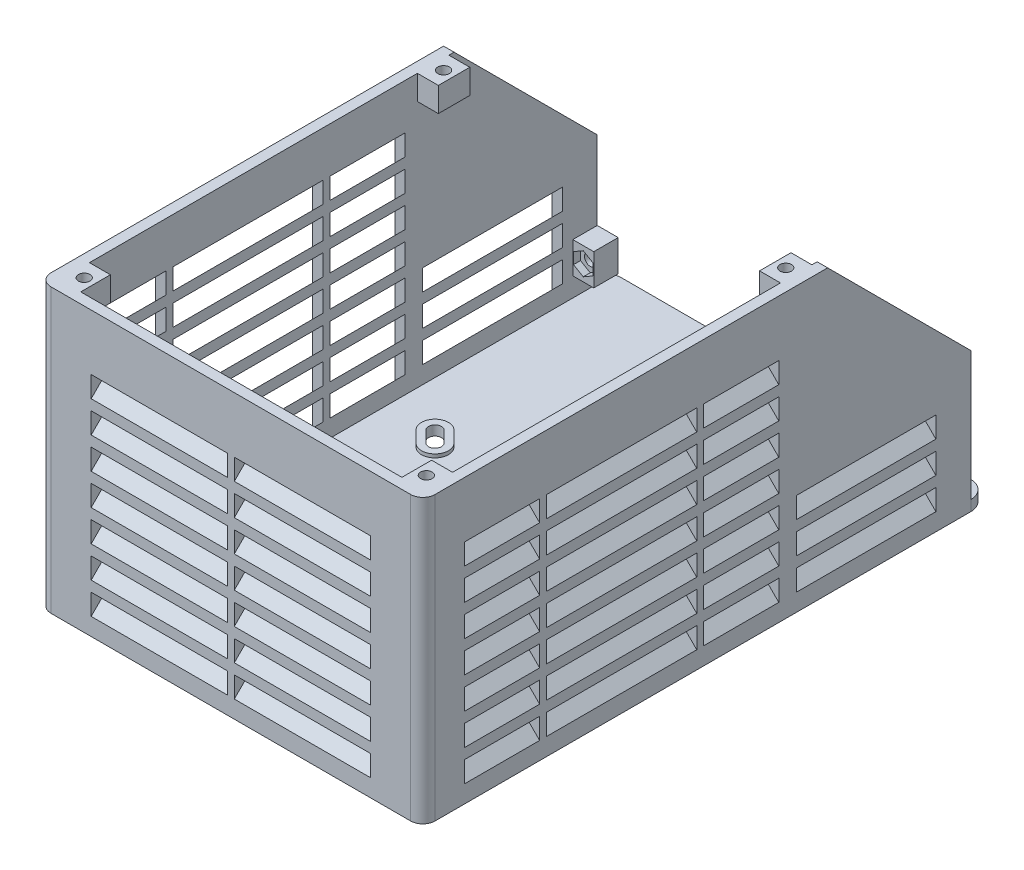
SolidWorks part; units mm, degrees
ref_plane "前视基准面" through (0, 0, 0) normal (0, 0, 1) x (1, 0, 0)
ref_plane "上视基准面" through (0, 0, 0) normal (0, 1, 0) x (1, 0, 0)
ref_plane "右视基准面" through (0, 0, 0) normal (1, 0, 0) x (0, 0, -1)
sketch "草图2" plane through (0, 0, 0) normal (0, 1, 0) x (1, 0, 0)
  line L5 (-55, -80.9767) -> (55, -80.9767)
  line L6 (-55, -80.9767) -> (-55, 80.9767)
  line L7 (-37.4767, -59.9767) -> (37.4767, -59.9767) construction
  line L8 (-37.4767, -59.9767) -> (-37.4767, 14.9767) construction
  line L9 (-37.4767, 14.9767) -> (37.4767, 14.9767) construction
  line L10 (37.4767, -59.9767) -> (37.4767, 14.9767) construction
  line L11 (-37.4767, -59.9767) -> (37.4767, 14.9767) construction
  line L12 (-37.4767, 14.9767) -> (37.4767, -59.9767) construction
  line L13 (-55, 80.9767) -> (55, 80.9767)
  line L14 (55, -80.9767) -> (55, 80.9767)
  line L15 (-55, -80.9767) -> (55, 80.9767) construction
  line L16 (-55, 80.9767) -> (55, -80.9767) construction
  circle A0 centre (-37.4767, 14.9767) radius 1.75
  circle A1 centre (-37.4767, -59.9767) radius 1.75
  circle A2 centre (37.4767, -59.9767) radius 1.75
  circle A3 centre (37.4767, 14.9767) radius 1.75
  point P0 (0, 0)
  point P6 (0, -22.5)
  dimension "D2" = 3.5
  dimension "D1" = 106
  dimension "D3" = 66
  dimension "D4" = 110
  dimension "D5" = 21
extrude "凸台-拉伸1" add sketch "草图2" along normal blind 3
fillet "圆角1" radius 3.5 2 edges at (-55, 1.5, 80.9767) (55, 1.5, 80.9767)
fillet "圆角2" radius 5 2 edges at (-55, 1.5, -80.9767) (55, 1.5, -80.9767)
sketch "草图3" plane through (0, 3, 0) normal (0, 1, 0) x (1, 0, 0)
  line L7 (-55, 75.9767) -> (-55, -77.4767) construction
  line L17 (55, -77.4767) -> (55, 75.9767) construction
  line L18 (-51.5, -80.9767) -> (51.5, -80.9767) construction
  line L19 (-52, 75.9767) -> (-52, -77.4767)
  line L20 (52, -77.4767) -> (52, 75.9767)
  line L21 (-51.5, -77.9767) -> (51.5, -77.9767)
  line L22 (-52, 75.9767) -> (-52, -77.4767)
  line L23 (52, -77.4767) -> (52, 75.9767)
  line L24 (-51.5, -77.9767) -> (51.5, -77.9767)
  line L25 (-55, 75.9767) -> (-55, -77.4767)
  line L26 (55, -77.4767) -> (55, 75.9767)
  line L27 (-51.5, -80.9767) -> (51.5, -80.9767)
  line L28 (55, 75.9767) -> (52, 75.9767)
  line L29 (-52, 75.9767) -> (-55, 75.9767)
  arc A2 (-55, -77.4767) -> (-51.5, -80.9767) centre (-51.5, -77.4767) ccw construction
  arc A3 (51.5, -80.9767) -> (55, -77.4767) centre (51.5, -77.4767) ccw construction
  arc A4 (-52, -77.4767) -> (-51.5, -77.9767) centre (-51.5, -77.4767) ccw
  arc A5 (51.5, -77.9767) -> (52, -77.4767) centre (51.5, -77.4767) ccw
  arc A6 (-52, -77.4767) -> (-51.5, -77.9767) centre (-51.5, -77.4767) ccw
  arc A7 (51.5, -77.9767) -> (52, -77.4767) centre (51.5, -77.4767) ccw
  arc A8 (-55, -77.4767) -> (-51.5, -80.9767) centre (-51.5, -77.4767) ccw
  arc A9 (51.5, -80.9767) -> (55, -77.4767) centre (51.5, -77.4767) ccw
  dimension "D1" = 3
extrude "凸台-拉伸2" add sketch "草图3" along normal blind 78
sketch "草图4" plane through (55, 0, 0) normal (1, 0, 0) x (0, 0, -1)
  line L0 (75.9767, 81) -> (75.9767, 39.9878)
  line L1 (75.9767, 81) -> (75.9767, 3) construction
  line L2 (75.9767, 39.9878) -> (34.9645, 81)
  line L3 (-77.4767, 81) -> (75.9767, 81) construction
  line L4 (34.9645, 81) -> (75.9767, 81)
  dimension "D1" = 45
  dimension "D2" = 58
extrude "切除-拉伸1" cut sketch "草图4" against normal through all
sketch "草图16" plane through (0, 0, 0) normal (0, -1, 0) x (1, 0, 0)
  line L0 (-37.9716, 60.4716) -> (-34.7897, 57.2897) construction
  line L4 (-36.6635, 61.7798) -> (-33.4815, 58.5978)
  line L5 (-39.2798, 59.1635) -> (-36.0978, 55.9815)
  line L6 (-37.4767, 59.9767) -> (37.4767, -14.9767) construction
  line L7 (37.9716, 60.4716) -> (34.7897, 57.2897) construction
  line L8 (39.2798, 59.1635) -> (36.0978, 55.9815)
  line L9 (36.6635, 61.7798) -> (33.4815, 58.5978)
  line L10 (37.9716, -15.4716) -> (34.7897, -12.2897) construction
  line L11 (36.6635, -16.7798) -> (33.4815, -13.5978)
  line L12 (39.2798, -14.1635) -> (36.0978, -10.9815)
  line L13 (-37.9716, -15.4716) -> (-34.7897, -12.2897) construction
  line L14 (-39.2798, -14.1635) -> (-36.0978, -10.9815)
  line L15 (-36.6635, -16.7798) -> (-33.4815, -13.5978)
  line L16 (0, 22.5) -> (-37.9716, 60.4716) construction
  arc A2 (-36.6635, 61.7798) -> (-39.2798, 59.1635) centre (-37.9716, 60.4716) ccw
  arc A3 (-36.0978, 55.9815) -> (-33.4815, 58.5978) centre (-34.7897, 57.2897) ccw
  circle A5 centre (-37.4767, 59.9767) radius 1.75 construction
  arc A6 (39.2798, 59.1635) -> (36.6635, 61.7798) centre (37.9716, 60.4716) ccw
  arc A7 (33.4815, 58.5978) -> (36.0978, 55.9815) centre (34.7897, 57.2897) ccw
  arc A8 (36.6635, -16.7798) -> (39.2798, -14.1635) centre (37.9716, -15.4716) ccw
  arc A9 (36.0978, -10.9815) -> (33.4815, -13.5978) centre (34.7897, -12.2897) ccw
  arc A10 (-39.2798, -14.1635) -> (-36.6635, -16.7798) centre (-37.9716, -15.4716) ccw
  arc A11 (-33.4815, -13.5978) -> (-36.0978, -10.9815) centre (-34.7897, -12.2897) ccw
  point P2 (-36.3806, 58.8806)
  point P18 (36.3806, 58.8806)
  point P25 (36.3806, -13.8806)
  point P32 (-36.3806, -13.8806)
  dimension "D3" = 0.1
  dimension "D1" = 0.7
  dimension "D2" = 4.5
  dimension "D5" = 53.7
  dimension "D4" = 4
extrude "切除-拉伸8" cut sketch "草图16" against normal through all
sketch "草图9" plane through (0, 3, 0) normal (0, 1, 0) x (1, 0, 0)
  line L0 (39.2798, 14.1635) -> (36.0978, 10.9815) construction
  line L1 (33.4815, 13.5978) -> (36.6635, 16.7798) construction
  line L2 (-36.0978, 10.9815) -> (-39.2798, 14.1635) construction
  line L3 (-36.6635, 16.7798) -> (-33.4815, 13.5978) construction
  line L4 (39.2798, 14.1635) -> (36.0978, 10.9815)
  line L5 (33.4815, 13.5978) -> (36.6635, 16.7798)
  line L6 (-36.0978, 10.9815) -> (-39.2798, 14.1635)
  line L7 (-36.6635, 16.7798) -> (-33.4815, 13.5978)
  line L8 (36.0978, -55.9815) -> (39.2798, -59.1635) construction
  line L9 (36.6635, -61.7798) -> (33.4815, -58.5978) construction
  line L10 (-39.2798, -59.1635) -> (-36.0978, -55.9815) construction
  line L11 (-33.4815, -58.5978) -> (-36.6635, -61.7798) construction
  line L12 (36.0978, -55.9815) -> (39.2798, -59.1635)
  line L13 (36.6635, -61.7798) -> (33.4815, -58.5978)
  line L14 (-39.2798, -59.1635) -> (-36.0978, -55.9815)
  line L15 (-33.4815, -58.5978) -> (-36.6635, -61.7798)
  line L16 (40.694, 12.7493) -> (37.512, 9.5673)
  line L17 (32.0673, 15.012) -> (35.2493, 18.194)
  line L18 (-37.512, 9.5673) -> (-40.694, 12.7493)
  line L19 (-35.2493, 18.194) -> (-32.0673, 15.012)
  line L20 (37.512, -54.5673) -> (40.694, -57.7493)
  line L21 (35.2493, -63.194) -> (32.0673, -60.012)
  line L22 (-40.694, -57.7493) -> (-37.512, -54.5673)
  line L23 (-32.0673, -60.012) -> (-35.2493, -63.194)
  arc A12 (33.4815, 13.5978) -> (36.0978, 10.9815) centre (34.7897, 12.2897) ccw construction
  arc A13 (39.2798, 14.1635) -> (36.6635, 16.7798) centre (37.9716, 15.4716) ccw construction
  arc A14 (-36.0978, 10.9815) -> (-33.4815, 13.5978) centre (-34.7897, 12.2897) ccw construction
  arc A15 (-36.6635, 16.7798) -> (-39.2798, 14.1635) centre (-37.9716, 15.4716) ccw construction
  arc A16 (33.4815, 13.5978) -> (36.0978, 10.9815) centre (34.7897, 12.2897) ccw
  arc A17 (39.2798, 14.1635) -> (36.6635, 16.7798) centre (37.9716, 15.4716) ccw
  arc A18 (-36.0978, 10.9815) -> (-33.4815, 13.5978) centre (-34.7897, 12.2897) ccw
  arc A19 (-36.6635, 16.7798) -> (-39.2798, 14.1635) centre (-37.9716, 15.4716) ccw
  arc A20 (36.6635, -61.7798) -> (39.2798, -59.1635) centre (37.9716, -60.4716) ccw construction
  arc A21 (36.0978, -55.9815) -> (33.4815, -58.5978) centre (34.7897, -57.2897) ccw construction
  arc A22 (-39.2798, -59.1635) -> (-36.6635, -61.7798) centre (-37.9716, -60.4716) ccw construction
  arc A23 (-33.4815, -58.5978) -> (-36.0978, -55.9815) centre (-34.7897, -57.2897) ccw construction
  arc A24 (36.6635, -61.7798) -> (39.2798, -59.1635) centre (37.9716, -60.4716) ccw
  arc A25 (36.0978, -55.9815) -> (33.4815, -58.5978) centre (34.7897, -57.2897) ccw
  arc A26 (-39.2798, -59.1635) -> (-36.6635, -61.7798) centre (-37.9716, -60.4716) ccw
  arc A27 (-33.4815, -58.5978) -> (-36.0978, -55.9815) centre (-34.7897, -57.2897) ccw
  arc A28 (32.0673, 15.012) -> (37.512, 9.5673) centre (34.7897, 12.2897) ccw
  arc A29 (40.694, 12.7493) -> (35.2493, 18.194) centre (37.9716, 15.4716) ccw
  arc A30 (-35.2493, 18.194) -> (-40.694, 12.7493) centre (-37.9716, 15.4716) ccw
  arc A31 (-37.512, 9.5673) -> (-32.0673, 15.012) centre (-34.7897, 12.2897) ccw
  arc A32 (35.2493, -63.194) -> (40.694, -57.7493) centre (37.9716, -60.4716) ccw
  arc A33 (37.512, -54.5673) -> (32.0673, -60.012) centre (34.7897, -57.2897) ccw
  arc A34 (-32.0673, -60.012) -> (-37.512, -54.5673) centre (-34.7897, -57.2897) ccw
  arc A35 (-40.694, -57.7493) -> (-35.2493, -63.194) centre (-37.9716, -60.4716) ccw
  dimension "D1" = 2
sketch "草图17" plane through (0, 0, 0) normal (0, -1, 0) x (1, 0, 0)
  line L0 (33.4815, -13.5978) -> (36.6635, -16.7798) construction
  line L1 (39.2798, -14.1635) -> (36.0978, -10.9815) construction
  line L2 (-36.0978, -10.9815) -> (-39.2798, -14.1635) construction
  line L3 (-36.6635, -16.7798) -> (-33.4815, -13.5978) construction
  line L4 (36.0978, 55.9815) -> (39.2798, 59.1635) construction
  line L5 (36.6635, 61.7798) -> (33.4815, 58.5978) construction
  line L6 (-39.2798, 59.1635) -> (-36.0978, 55.9815) construction
  line L7 (-33.4815, 58.5978) -> (-36.6635, 61.7798) construction
  line L8 (33.4815, -13.5978) -> (36.6635, -16.7798)
  line L9 (39.2798, -14.1635) -> (36.0978, -10.9815)
  line L10 (-36.0978, -10.9815) -> (-39.2798, -14.1635)
  line L11 (-36.6635, -16.7798) -> (-33.4815, -13.5978)
  line L12 (36.0978, 55.9815) -> (39.2798, 59.1635)
  line L13 (36.6635, 61.7798) -> (33.4815, 58.5978)
  line L14 (-39.2798, 59.1635) -> (-36.0978, 55.9815)
  line L15 (-33.4815, 58.5978) -> (-36.6635, 61.7798)
  line L16 (32.2794, -14.7999) -> (35.4614, -17.9819)
  line L17 (40.4819, -12.9614) -> (37.2999, -9.7794)
  line L18 (-37.2999, -9.7794) -> (-40.4819, -12.9614)
  line L19 (-35.4614, -17.9819) -> (-32.2794, -14.7999)
  line L20 (37.2999, 54.7794) -> (40.4819, 57.9614)
  line L21 (35.4614, 62.9819) -> (32.2794, 59.7999)
  line L22 (-40.4819, 57.9614) -> (-37.2999, 54.7794)
  line L23 (-32.2794, 59.7999) -> (-35.4614, 62.9819)
  arc A0 (36.6635, -16.7798) -> (39.2798, -14.1635) centre (37.9716, -15.4716) ccw construction
  arc A1 (36.0978, -10.9815) -> (33.4815, -13.5978) centre (34.7897, -12.2897) ccw construction
  arc A2 (-39.2798, -14.1635) -> (-36.6635, -16.7798) centre (-37.9716, -15.4716) ccw construction
  arc A3 (-33.4815, -13.5978) -> (-36.0978, -10.9815) centre (-34.7897, -12.2897) ccw construction
  arc A4 (39.2798, 59.1635) -> (36.6635, 61.7798) centre (37.9716, 60.4716) ccw construction
  arc A5 (33.4815, 58.5978) -> (36.0978, 55.9815) centre (34.7897, 57.2897) ccw construction
  arc A6 (-36.0978, 55.9815) -> (-33.4815, 58.5978) centre (-34.7897, 57.2897) ccw construction
  arc A7 (-36.6635, 61.7798) -> (-39.2798, 59.1635) centre (-37.9716, 60.4716) ccw construction
  arc A8 (36.6635, -16.7798) -> (39.2798, -14.1635) centre (37.9716, -15.4716) ccw
  arc A9 (36.0978, -10.9815) -> (33.4815, -13.5978) centre (34.7897, -12.2897) ccw
  arc A10 (-39.2798, -14.1635) -> (-36.6635, -16.7798) centre (-37.9716, -15.4716) ccw
  arc A11 (-33.4815, -13.5978) -> (-36.0978, -10.9815) centre (-34.7897, -12.2897) ccw
  arc A12 (39.2798, 59.1635) -> (36.6635, 61.7798) centre (37.9716, 60.4716) ccw
  arc A13 (33.4815, 58.5978) -> (36.0978, 55.9815) centre (34.7897, 57.2897) ccw
  arc A14 (-36.0978, 55.9815) -> (-33.4815, 58.5978) centre (-34.7897, 57.2897) ccw
  arc A15 (-36.6635, 61.7798) -> (-39.2798, 59.1635) centre (-37.9716, 60.4716) ccw
  arc A16 (35.4614, -17.9819) -> (40.4819, -12.9614) centre (37.9716, -15.4716) ccw
  arc A17 (37.2999, -9.7794) -> (32.2794, -14.7999) centre (34.7897, -12.2897) ccw
  arc A18 (-40.4819, -12.9614) -> (-35.4614, -17.9819) centre (-37.9716, -15.4716) ccw
  arc A19 (-32.2794, -14.7999) -> (-37.2999, -9.7794) centre (-34.7897, -12.2897) ccw
  arc A20 (40.4819, 57.9614) -> (35.4614, 62.9819) centre (37.9716, 60.4716) ccw
  arc A21 (32.2794, 59.7999) -> (37.2999, 54.7794) centre (34.7897, 57.2897) ccw
  arc A22 (-37.2999, 54.7794) -> (-32.2794, 59.7999) centre (-34.7897, 57.2897) ccw
  arc A23 (-35.4614, 62.9819) -> (-40.4819, 57.9614) centre (-37.9716, 60.4716) ccw
  dimension "D1" = 1.7
extrude "切除-拉伸9" cut sketch "草图17" against normal blind 1.2
ref_plane "基准面4" through (0, 0, -20.9767) normal (0, 0, -1) x (-1, 0, 0)
sketch "草图6" plane through (0, 0, -20.9767) normal (0, 0, -1) x (-1, 0, 0)
  line L0 (-55, 65) -> (-52, 68)
  line L1 (-55, 65) -> (-55, 59)
  line L2 (-52, 68) -> (-52, 62)
  line L3 (-55, 59) -> (-52, 62)
  line L4 (-55, 81) -> (-55, 39.9878) construction
  line L5 (-52, 81) -> (-52, 3) construction
  line L6 (-52, 81) -> (-52, 39.9878) construction
  line L7 (-52, 81) -> (-55, 81) construction
  line L44 (0, 0) -> (0, 83.4233) construction
  line L85 (-55, 56) -> (-55, 50)
  line L86 (-55, 56) -> (-52, 59)
  line L87 (-52, 59) -> (-52, 53)
  line L88 (-55, 50) -> (-52, 53)
  line L89 (-55, 47) -> (-55, 41)
  line L90 (-55, 47) -> (-52, 50)
  line L91 (-52, 50) -> (-52, 44)
  line L92 (-55, 41) -> (-52, 44)
  line L93 (-55, 38) -> (-55, 32)
  line L94 (-55, 38) -> (-52, 41)
  line L95 (-52, 41) -> (-52, 35)
  line L96 (-55, 32) -> (-52, 35)
  line L97 (-55, 29) -> (-55, 23)
  line L98 (-55, 29) -> (-52, 32)
  line L99 (-52, 32) -> (-52, 26)
  line L100 (-55, 23) -> (-52, 26)
  line L101 (-55, 20) -> (-55, 14)
  line L102 (-55, 20) -> (-52, 23)
  line L103 (-52, 23) -> (-52, 17)
  line L104 (-55, 14) -> (-52, 17)
  line L105 (-55, 11) -> (-55, 5)
  line L106 (-55, 11) -> (-52, 14)
  line L107 (-52, 14) -> (-52, 8)
  line L108 (-55, 5) -> (-52, 8)
  line L109 (55, 5) -> (52, 8)
  line L110 (52, 14) -> (52, 8)
  line L111 (55, 11) -> (52, 14)
  line L112 (55, 11) -> (55, 5)
  line L113 (55, 14) -> (52, 17)
  line L114 (52, 23) -> (52, 17)
  line L115 (55, 20) -> (52, 23)
  line L116 (55, 20) -> (55, 14)
  line L117 (55, 23) -> (52, 26)
  line L118 (52, 32) -> (52, 26)
  line L119 (55, 29) -> (52, 32)
  line L120 (55, 29) -> (55, 23)
  line L121 (55, 32) -> (52, 35)
  line L122 (52, 41) -> (52, 35)
  line L123 (55, 38) -> (52, 41)
  line L124 (55, 38) -> (55, 32)
  line L125 (55, 41) -> (52, 44)
  line L126 (52, 50) -> (52, 44)
  line L127 (55, 47) -> (52, 50)
  line L128 (55, 47) -> (55, 41)
  line L129 (55, 50) -> (52, 53)
  line L130 (52, 59) -> (52, 53)
  line L131 (55, 56) -> (52, 59)
  line L132 (55, 56) -> (55, 50)
  line L133 (55, 59) -> (52, 62)
  line L134 (52, 68) -> (52, 62)
  line L135 (55, 65) -> (55, 59)
  line L136 (55, 65) -> (52, 68)
  dimension "D1" = 6
  dimension "D2" = 135
  dimension "D3" = 16
  dimension "D4" = 7
extrude "切除-拉伸2" cut sketch "草图6" against normal blind 90
sketch "草图8" plane through (0, 0, 0) normal (1, 0, 0) x (0, 0, -1)
  line L0 (-80.9767, 65) -> (-77.9767, 68)
  line L1 (-80.9767, 65) -> (-80.9767, 59)
  line L2 (-77.9767, 68) -> (-77.9767, 62)
  line L3 (-80.9767, 59) -> (-77.9767, 62)
  line L4 (-80.9767, 0) -> (-80.9767, 81) construction
  line L42 (-69.0233, 65) -> (20.9767, 65) construction
  line L43 (-77.9767, 59) -> (-77.9767, 53)
  line L44 (-80.9767, 56) -> (-77.9767, 59)
  line L45 (-80.9767, 56) -> (-80.9767, 50)
  line L46 (-80.9767, 50) -> (-77.9767, 53)
  line L47 (-77.9767, 50) -> (-77.9767, 44)
  line L48 (-80.9767, 47) -> (-77.9767, 50)
  line L49 (-80.9767, 47) -> (-80.9767, 41)
  line L50 (-80.9767, 41) -> (-77.9767, 44)
  line L51 (-77.9767, 41) -> (-77.9767, 35)
  line L52 (-80.9767, 38) -> (-77.9767, 41)
  line L53 (-80.9767, 38) -> (-80.9767, 32)
  line L54 (-80.9767, 32) -> (-77.9767, 35)
  line L55 (-77.9767, 32) -> (-77.9767, 26)
  line L56 (-80.9767, 29) -> (-77.9767, 32)
  line L57 (-80.9767, 29) -> (-80.9767, 23)
  line L58 (-80.9767, 23) -> (-77.9767, 26)
  line L59 (-77.9767, 23) -> (-77.9767, 17)
  line L60 (-80.9767, 20) -> (-77.9767, 23)
  line L61 (-80.9767, 20) -> (-80.9767, 14)
  line L62 (-80.9767, 14) -> (-77.9767, 17)
  line L63 (-77.9767, 14) -> (-77.9767, 8)
  line L64 (-80.9767, 11) -> (-77.9767, 14)
  line L65 (-80.9767, 11) -> (-80.9767, 5)
  line L66 (-80.9767, 5) -> (-77.9767, 8)
  dimension "D1" = 6
  dimension "D2" = 3
  dimension "D3" = 7
  dimension "D4" = 135
extrude "切除-拉伸3" cut sketch "草图8" against normal mid plane 80
ref_plane "基准面5" through (0, 0, -65.9767) normal (0, 0, -1) x (-1, 0, 0)
sketch "草图15" plane through (0, 0, -65.9767) normal (0, 0, -1) x (-1, 0, 0)
  line L0 (-52, 14) -> (-55, 11)
  line L1 (-52, 14) -> (-52, 8)
  line L2 (-55, 11) -> (-55, 5)
  line L3 (-52, 8) -> (-55, 5)
  line L4 (-52, 39.9878) -> (-52, 3) construction
  line L5 (-55, 39.9878) -> (-55, 3) construction
  line L6 (40, 8) -> (-40, 8) construction
  line L7 (-55, 20) -> (-55, 14)
  line L8 (-52, 23) -> (-55, 20)
  line L9 (-52, 23) -> (-52, 17)
  line L10 (-52, 17) -> (-55, 14)
  line L11 (-55, 29) -> (-55, 23)
  line L12 (-52, 32) -> (-55, 29)
  line L13 (-52, 32) -> (-52, 26)
  line L14 (-52, 26) -> (-55, 23)
  line L15 (0, 0) -> (0, 37.0464) construction
  line L16 (52, 26) -> (55, 23)
  line L17 (52, 32) -> (52, 26)
  line L18 (52, 32) -> (55, 29)
  line L19 (55, 29) -> (55, 23)
  line L20 (52, 17) -> (55, 14)
  line L21 (52, 23) -> (52, 17)
  line L22 (52, 23) -> (55, 20)
  line L23 (55, 20) -> (55, 14)
  line L24 (52, 8) -> (55, 5)
  line L25 (55, 11) -> (55, 5)
  line L26 (52, 14) -> (52, 8)
  line L27 (52, 14) -> (55, 11)
  dimension "D1" = 6
  dimension "D2" = 135
  dimension "D3" = 3
extrude "切除-拉伸7" cut sketch "草图15" against normal blind 40
sketch "草图7" plane through (0, 3, 0) normal (0, 1, 0) x (1, 0, 0)
  line L0 (64.059, -69.0233) -> (64.059, -24.0233) construction
  line L6 (64.059, -24.0233) -> (64.059, 20.9767) construction
  line L7 (55, -69.0233) -> (52, -69.0233) construction
  line L8 (55, 20.9767) -> (52, 20.9767) construction
  line L9 (52, 34.9645) -> (52, -77.4767) construction
  line L10 (52, -47.5233) -> (55, -47.5233)
  line L11 (52, -47.5233) -> (52, -45.5233)
  line L12 (52, -45.5233) -> (55, -45.5233)
  line L13 (55, -47.5233) -> (55, -45.5233)
  line L14 (55, -77.4767) -> (55, 34.9645) construction
  line L15 (0, 0) -> (0, -45.6831) construction
  line L16 (52, -2.5233) -> (55, -2.5233)
  line L17 (52, -2.5233) -> (52, -0.5233)
  line L18 (52, -0.5233) -> (55, -0.5233)
  line L19 (55, -2.5233) -> (55, -0.5233)
  line L20 (-55, -47.5233) -> (-55, -45.5233)
  line L21 (-52, -45.5233) -> (-55, -45.5233)
  line L22 (-52, -47.5233) -> (-52, -45.5233)
  line L23 (-52, -47.5233) -> (-55, -47.5233)
  line L24 (-55, -2.5233) -> (-55, -0.5233)
  line L25 (-52, -0.5233) -> (-55, -0.5233)
  line L26 (-52, -2.5233) -> (-52, -0.5233)
  line L27 (-52, -2.5233) -> (-55, -2.5233)
  line L28 (51.5, -77.9767) -> (-51.5, -77.9767) construction
  line L29 (-1, -77.9767) -> (1, -77.9767)
  line L30 (-1, -77.9767) -> (-1, -80.9767)
  line L31 (-1, -80.9767) -> (1, -80.9767)
  line L32 (1, -77.9767) -> (1, -80.9767)
  line L33 (-51.5, -80.9767) -> (51.5, -80.9767) construction
  point P21 (55, -46.5233)
  point P22 (64.059, -46.5233)
  point P23 (55, -1.5233)
  point P24 (64.059, -1.5233)
  point P44 (0, -77.9767)
  dimension "D1" = 2
  dimension "D2" = 2
extrude "凸台-拉伸3" add sketch "草图7" along normal through all
sketch "草图10" plane through (0, 0, 0) normal (0, -1, 0) x (1, 0, 0)
  line L0 (-51.5, 80.9767) -> (51.5, 80.9767) construction
  line L1 (-45, -70.9767) -> (45, -70.9767) construction
  line L2 (-45, -70.9767) -> (-45, 70.9767) construction
  line L3 (-45, 70.9767) -> (45, 70.9767) construction
  line L4 (45, -70.9767) -> (45, 70.9767) construction
  line L5 (-45, -70.9767) -> (45, 70.9767) construction
  line L6 (-45, 70.9767) -> (45, -70.9767) construction
  line L7 (55, 77.4767) -> (55, -75.9767) construction
  circle A0 centre (-45, 70.9767) radius 5.5
  circle A1 centre (45, 70.9767) radius 5.5
  circle A2 centre (45, -70.9767) radius 5.5
  circle A3 centre (-45, -70.9767) radius 5.5
  point P0 (0, 0)
  dimension "D3" = 11
  dimension "D1" = 10
  dimension "D2" = 10
extrude "凸台-拉伸7" add sketch "草图9" along normal blind 1
extrude "切除-拉伸4" cut sketch "草图10" against normal blind 0.8
sketch "草图11" plane through (0, 81, 0) normal (0, 1, 0) x (1, 0, 0)
  line L0 (51.5, -77.9767) -> (-51.5, -77.9767) construction
  line L1 (49, -73.9767) -> (-49, -73.9767) construction
  line L2 (49, -73.9767) -> (49, 28.9645) construction
  line L3 (49, 28.9645) -> (-49, 28.9645) construction
  line L4 (-49, -73.9767) -> (-49, 28.9645) construction
  line L5 (49, -73.9767) -> (-49, 28.9645) construction
  line L6 (49, 28.9645) -> (-49, -73.9767) construction
  line L7 (52, 34.9645) -> (52, -77.4767) construction
  line L8 (52, 34.9645) -> (55, 34.9645) construction
  line L9 (-52, -77.4767) -> (-52, 34.9645) construction
  line L10 (-46, 24.4645) -> (-52, 24.4645)
  line L11 (-46, 24.4645) -> (-46, 33.4645)
  line L12 (-46, 33.4645) -> (-52, 33.4645)
  line L13 (-52, 24.4645) -> (-52, 33.4645)
  line L14 (-46, 24.4645) -> (-52, 33.4645) construction
  line L15 (-46, 33.4645) -> (-52, 24.4645) construction
  line L16 (-52, -77.4767) -> (-52, 75.9767) construction
  line L17 (46, 24.4645) -> (52, 24.4645)
  line L18 (46, 24.4645) -> (46, 33.4645)
  line L19 (46, 33.4645) -> (52, 33.4645)
  line L20 (52, 24.4645) -> (52, 33.4645)
  line L21 (46, 24.4645) -> (52, 33.4645) construction
  line L22 (46, 33.4645) -> (52, 24.4645) construction
  line L23 (46, -69.4767) -> (52, -69.4767)
  line L24 (46, -69.4767) -> (46, -78.4767)
  line L25 (46, -78.4767) -> (52, -78.4767)
  line L26 (52, -69.4767) -> (52, -78.4767)
  line L27 (46, -69.4767) -> (52, -78.4767) construction
  line L28 (46, -78.4767) -> (52, -69.4767) construction
  line L29 (-46, -78.4767) -> (-52, -78.4767)
  line L30 (-46, -78.4767) -> (-46, -69.4767)
  line L31 (-46, -69.4767) -> (-52, -69.4767)
  line L32 (-52, -78.4767) -> (-52, -69.4767)
  line L33 (-46, -78.4767) -> (-52, -69.4767) construction
  line L34 (-46, -69.4767) -> (-52, -78.4767) construction
  circle A0 centre (49, 28.9645) radius 1.65
  circle A1 centre (-49, 28.9645) radius 1.65
  circle A2 centre (-49, -73.9767) radius 1.65
  circle A3 centre (49, -73.9767) radius 1.65
  point P0 (0, -22.5061)
  dimension "D4" = 3.3
  dimension "D1" = 4
  dimension "D2" = 3
  dimension "D3" = 6
  dimension "D5" = 9
extrude "凸台-拉伸5" add sketch "草图11" against normal blind 7
sketch "草图12" plane through (0, 74, 0) normal (0, -1, 0) x (1, 0, 0)
  line L1 (-49, -32.1976) -> (-46.2, -30.581)
  line L2 (-46.2, -30.581) -> (-46.2, -27.3479)
  line L3 (-46.2, -27.3479) -> (-49, -25.7313)
  line L4 (-49, -25.7313) -> (-51.8, -27.3479)
  line L5 (-51.8, -27.3479) -> (-51.8, -30.581)
  line L6 (-51.8, -30.581) -> (-49, -32.1976)
  line L7 (49, -32.1976) -> (51.8, -30.581)
  line L8 (51.8, -30.581) -> (51.8, -27.3479)
  line L9 (51.8, -27.3479) -> (49, -25.7313)
  line L10 (49, -25.7313) -> (46.2, -27.3479)
  line L11 (46.2, -27.3479) -> (46.2, -30.581)
  line L12 (46.2, -30.581) -> (49, -32.1976)
  line L13 (-49, 70.7435) -> (-46.2, 72.3601)
  line L14 (-46.2, 72.3601) -> (-46.2, 75.5932)
  line L15 (-46.2, 75.5932) -> (-49, 77.2098)
  line L16 (-49, 77.2098) -> (-51.8, 75.5932)
  line L17 (-51.8, 75.5932) -> (-51.8, 72.3601)
  line L18 (-51.8, 72.3601) -> (-49, 70.7435)
  line L19 (49, 70.7435) -> (51.8, 72.3601)
  line L20 (51.8, 72.3601) -> (51.8, 75.5932)
  line L21 (51.8, 75.5932) -> (49, 77.2098)
  line L22 (49, 77.2098) -> (46.2, 75.5932)
  line L23 (46.2, 75.5932) -> (46.2, 72.3601)
  line L24 (46.2, 72.3601) -> (49, 70.7435)
  circle A0 centre (-49, -28.9645) radius 2.8 construction
  circle A1 centre (49, -28.9645) radius 2.8 construction
  circle A2 centre (-49, 73.9767) radius 2.8 construction
  circle A3 centre (49, 73.9767) radius 2.8 construction
  dimension "D1" = 5.6
extrude "切除-拉伸5" cut sketch "草图12" against normal blind 2
sketch "草图13" plane through (0, 0, -75.9767) normal (0, 0, -1) x (-1, 0, 0)
  line L0 (-49, 13) -> (49, 13) construction
  line L1 (-52, 74) -> (-52, 3) construction
  line L2 (-50, 3) -> (50, 3) construction
  line L3 (-52, 39.9878) -> (-52, 3) construction
  line L4 (-46, 8.5) -> (-52, 8.5)
  line L5 (-46, 8.5) -> (-46, 17.5)
  line L6 (-46, 17.5) -> (-52, 17.5)
  line L7 (-52, 8.5) -> (-52, 17.5)
  line L8 (-46, 8.5) -> (-52, 17.5) construction
  line L9 (-46, 17.5) -> (-52, 8.5) construction
  line L10 (52, 39.9878) -> (52, 3) construction
  line L11 (46, 8.5) -> (52, 8.5)
  line L12 (46, 8.5) -> (46, 17.5)
  line L13 (46, 17.5) -> (52, 17.5)
  line L14 (52, 8.5) -> (52, 17.5)
  line L15 (46, 8.5) -> (52, 17.5) construction
  line L16 (46, 17.5) -> (52, 8.5) construction
  circle A0 centre (-49, 13) radius 1.65
  circle A1 centre (49, 13) radius 1.65
  point P4 (0, 13)
  dimension "D1" = 3.3
  dimension "D2" = 3
  dimension "D3" = 10
  dimension "D4" = 9
extrude "凸台-拉伸6" add sketch "草图13" against normal blind 7
sketch "草图14" plane through (0, 0, -68.9767) normal (0, 0, 1) x (1, 0, 0)
  line L1 (46.2, 14.6166) -> (46.2, 11.3834)
  line L2 (46.2, 11.3834) -> (49, 9.7668)
  line L3 (49, 9.7668) -> (51.8, 11.3834)
  line L4 (51.8, 11.3834) -> (51.8, 14.6166)
  line L5 (51.8, 14.6166) -> (49, 16.2332)
  line L6 (49, 16.2332) -> (46.2, 14.6166)
  line L7 (-49, 16.2332) -> (-51.8, 14.6166)
  line L8 (-51.8, 14.6166) -> (-51.8, 11.3834)
  line L9 (-51.8, 11.3834) -> (-49, 9.7668)
  line L10 (-49, 9.7668) -> (-46.2, 11.3834)
  line L11 (-46.2, 11.3834) -> (-46.2, 14.6166)
  line L12 (-46.2, 14.6166) -> (-49, 16.2332)
  circle A0 centre (49, 13) radius 2.8 construction
  circle A1 centre (-49, 13) radius 2.8 construction
  dimension "D1" = 5.6
extrude "切除-拉伸6" cut sketch "草图14" against normal blind 2
